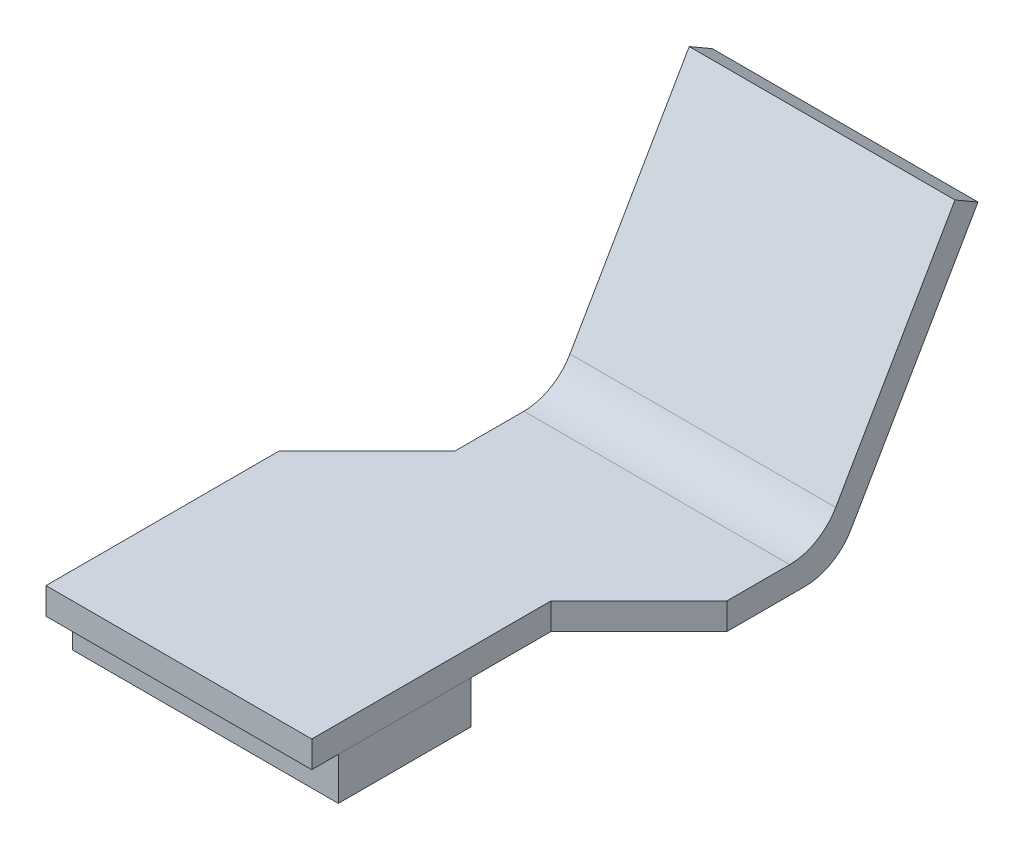
SolidWorks part; units mm, degrees
ref_plane "Front Plane" through (0, 0, 0) normal (0, 0, 1) x (1, 0, 0)
ref_plane "Top Plane" through (0, 0, 0) normal (0, 1, 0) x (1, 0, 0)
ref_plane "Right Plane" through (0, 0, 0) normal (1, 0, 0) x (0, 0, -1)
sketch "Sketch1" plane through (0, 0, 0) normal (1, 0, 0) x (0, 0, -1)
  line L0 (4.4879, 9.7733) -> (-0.5774, 1)
  line L1 (-0.5774, 1) -> (-16.4066, 1)
  line L3 (-16.4066, 0) -> (0, 0)
  line L4 (0, 0) -> (-0.5774, 1) construction
  line L5 (0, 0) -> (5.3539, 9.2733)
  line L12 (-16.4066, 0) -> (-16.4066, 1)
  line L13 (5.3539, 9.2733) -> (4.4879, 9.7733)
  dimension "D1" = 60
  dimension "D2" = 60
  dimension "D3" = 16.4066
  dimension "D4" = 10.7079
  dimension "D5" = 1
  dimension "D6" = 1
extrude "Boss-Extrude1" add sketch "Sketch1" along normal blind 13.31
sketch "Sketch2" plane through (0, 0, 0) normal (0, 1, 0) x (1, 0, 0)
  line L0 (13.31, -16.4066) -> (10, -16.4066)
  line L1 (13.31, -16.4066) -> (0, -16.4066) construction
  line L2 (10, -16.4066) -> (10, -7.4066)
  line L3 (10, -7.4066) -> (13.31, -4.0966)
  line L4 (13.31, -0.5774) -> (13.31, -16.4066) construction
  line L5 (13.31, -4.0966) -> (13.31, -16.4066)
  dimension "D1" = 45
  dimension "D3" = 9
  dimension "D4" = 10
extrude "Cut-Extrude1" cut sketch "Sketch2" along normal up to surface (1 mm away) up to face at (6.655, 1, 8.492)
fillet "Fillet1" radius 2 2 edges at (6.655, 1, 0.5774) (6.655, 0, 0)
sketch "Sketch4" plane through (0, 0, 0) normal (0, -1, 0) x (1, 0, 0)
  line L0 (0, 16.4066) -> (0, 1.1547) construction
  line L1 (0, 15.4066) -> (10, 15.4066)
  line L2 (0, 15.4066) -> (0, 10.4066)
  line L3 (0, 10.4066) -> (10, 10.4066)
  line L4 (10, 15.4066) -> (10, 10.4066)
  line L5 (10, 7.4066) -> (10, 16.4066) construction
  line L6 (10, 16.4066) -> (0, 16.4066) construction
  dimension "D1" = 1
  dimension "D2" = 10
  dimension "D3" = 5
extrude "Boss-Extrude2" add sketch "Sketch4" along normal blind 1.6 separate body
sketch "Sketch5" plane through (0, 0, 0) normal (0, 1, 0) x (1, 0, 0)
  line L0 (0, 5.3539) -> (0, -7.6461)
  line L1 (0, -1.7321) -> (0, -16.4066) construction
  line L2 (0, -7.6461) -> (3.31, -4.336)
  line L3 (3.31, -4.336) -> (3.31, 5.3539)
  line L4 (13.31, 5.3539) -> (0, 5.3539) construction
  line L5 (3.31, 5.3539) -> (0, 5.3539)
  line L6 (13.31, 4.4879) -> (13.31, 0) construction
  dimension "D1" = 10
  dimension "D2" = 13
  dimension "D3" = 45
extrude "Cut-Extrude2" cut sketch "Sketch5" against normal through all both and the other way through all
